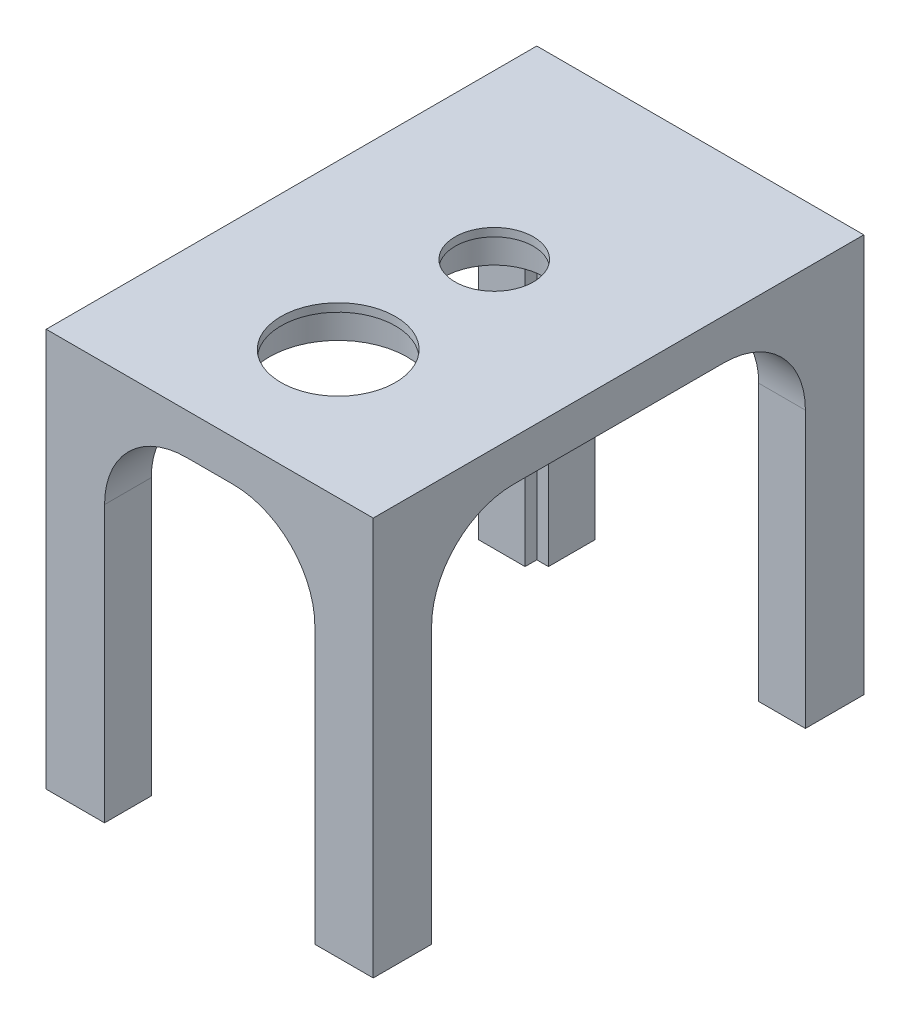
SolidWorks part; units mm, degrees
ref_plane "Front Plane" through (0, 0, 0) normal (0, 0, 1) x (1, 0, 0)
ref_plane "Top Plane" through (0, 0, 0) normal (0, 1, 0) x (1, 0, 0)
ref_plane "Right Plane" through (0, 0, 0) normal (1, 0, 0) x (0, 0, -1)
sketch "Sketch1" plane through (0, 0, 0) normal (0, 1, 0) x (1, 0, 0)
  line L1 (0, 0) -> (71.12, 0)
  line L2 (0, 0) -> (0, 106.68)
  line L3 (0, 106.68) -> (71.12, 106.68)
  line L4 (71.12, 0) -> (71.12, 106.68)
  dimension "D1" = 71.12
  dimension "D2" = 106.68
extrude "Boss-Extrude1" add sketch "Sketch1" along normal blind 87.884
shell "Shell1" thickness 10.16
sketch "Sketch3" plane through (0, 0, 0) normal (0, -1, 0) x (1, 0, 0)
  line L0 (0, 0) -> (71.12, 0) construction
  line L1 (0, -106.68) -> (0, 0) construction
  line L2 (6.35, -6.35) -> (6.35, -100.33) construction
  circle A0 centre (6.35, -6.35) radius 1.5875
  circle A1 centre (64.77, -6.35) radius 1.5875
  circle A2 centre (64.77, -100.33) radius 1.5875
  circle A3 centre (6.35, -100.33) radius 1.5875
  dimension "D1" = 6.35
  dimension "D2" = 6.35
  dimension "D5" = 93.98
  dimension "D3" = 2
  dimension "D4" = 2
extrude "Cut-Extrude1" cut sketch "Sketch3" against normal blind 10.16
sketch "Sketch4" plane through (0, 0, 0) normal (-1, 0, 0) x (0, 0, 1)
  line L0 (-106.68, 87.884) -> (0, 87.884) construction
  line L1 (-93.98, 0) -> (-12.7, 0)
  line L2 (-93.98, 0) -> (-93.98, 77.724)
  line L3 (-93.98, 77.724) -> (-12.7, 77.724)
  line L4 (-12.7, 0) -> (-12.7, 77.724)
  line L6 (0, 87.884) -> (0, 0) construction
  line L7 (-106.68, 87.884) -> (-106.68, 0) construction
  line L8 (-106.68, 0) -> (0, 0) construction
  dimension "D1" = 10.16
  dimension "D2" = 12.7
  dimension "D3" = 12.7
extrude "Cut-Extrude2" cut sketch "Sketch4" against normal through all
sketch "Sketch6" plane through (0, 0, 0) normal (0, -1, 0) x (1, 0, 0)
  line L0 (69.536, -6.35) -> (67.153, -2.2225)
  line L1 (11.116, -6.35) -> (8.733, -2.2225)
  line L2 (8.733, -2.2225) -> (3.967, -2.2225)
  line L3 (3.967, -2.2225) -> (1.584, -6.35)
  line L4 (1.584, -6.35) -> (3.967, -10.4775)
  line L5 (3.967, -10.4775) -> (8.733, -10.4775)
  line L6 (8.733, -10.4775) -> (11.116, -6.35)
  line L7 (67.153, -2.2225) -> (62.387, -2.2225)
  line L8 (62.387, -2.2225) -> (60.004, -6.35)
  line L9 (60.004, -6.35) -> (62.387, -10.4775)
  line L10 (62.387, -10.4775) -> (67.153, -10.4775)
  line L11 (67.153, -10.4775) -> (69.536, -6.35)
  line L12 (69.536, -100.33) -> (67.153, -96.2025)
  line L13 (67.153, -96.2025) -> (62.387, -96.2025)
  line L14 (62.387, -96.2025) -> (60.004, -100.33)
  line L15 (60.004, -100.33) -> (62.387, -104.4575)
  line L16 (62.387, -104.4575) -> (67.153, -104.4575)
  line L17 (67.153, -104.4575) -> (69.536, -100.33)
  line L18 (11.116, -100.33) -> (8.733, -96.2025)
  line L19 (8.733, -96.2025) -> (3.967, -96.2025)
  line L20 (3.967, -96.2025) -> (1.584, -100.33)
  line L21 (1.584, -100.33) -> (3.967, -104.4575)
  line L22 (3.967, -104.4575) -> (8.733, -104.4575)
  line L23 (8.733, -104.4575) -> (11.116, -100.33)
  circle A0 centre (6.35, -6.35) radius 4.1275 construction
  circle A1 centre (64.77, -6.35) radius 4.1275 construction
  circle A2 centre (64.77, -100.33) radius 4.1275 construction
  circle A3 centre (6.35, -100.33) radius 4.1275 construction
  dimension "D1" = 8.255
  dimension "D2" = 2
  dimension "D3" = 2
extrude "Cut-Extrude3" cut sketch "Sketch6" against normal blind 3.175
sketch "Sketch7" plane through (0, 0, -106.68) normal (0, 0, -1) x (-1, 0, 0)
  line L0 (-71.12, 87.884) -> (0, 87.884) construction
  line L1 (-58.42, 0) -> (-12.7, 0)
  line L2 (-58.42, 0) -> (-58.42, 77.724)
  line L3 (-58.42, 77.724) -> (-12.7, 77.724)
  line L4 (-12.7, 0) -> (-12.7, 77.724)
  line L6 (-71.12, 87.884) -> (-71.12, 0) construction
  line L7 (0, 87.884) -> (0, 0) construction
  dimension "D1" = 10.16
  dimension "D2" = 12.7
  dimension "D3" = 12.7
extrude "Cut-Extrude4" cut sketch "Sketch7" against normal through all and the other way through all
sketch "Sketch9" plane through (0, 87.884, 0) normal (0, 1, 0) x (1, 0, 0)
  line L1 (0, 0) -> (71.12, 0)
  line L2 (0, 0) -> (0, 106.68)
  line L3 (0, 106.68) -> (71.12, 106.68)
  line L4 (71.12, 0) -> (71.12, 106.68)
extrude "Cut-Extrude6" cut sketch "Sketch9" against normal blind 1.27
sketch "Sketch10" plane through (0, 77.724, 0) normal (0, -1, 0) x (-1, 0, 0)
  line L1 (-12.7, 0) -> (-58.42, 0) construction
  circle A0 centre (-35.56, 27.94) radius 14.986
  circle A1 centre (-35.56, 61.8744) radius 11.049
  point P4 (-35.56, 0)
  dimension "D1" = 29.972
  dimension "D3" = 22.098
  dimension "D2" = 27.94
  dimension "D4" = 33.9344
extrude "Cut-Extrude7" cut sketch "Sketch10" against normal blind 7.112
sketch "Sketch11" plane through (0, 77.724, 0) normal (0, -1, 0) x (1, 0, 0)
  circle A0 centre (35.56, -27.94) radius 12.446
  circle A1 centre (35.56, -61.8744) radius 8.509
  circle A2 centre (35.56, -27.94) radius 14.986 construction
  circle A3 centre (35.56, -61.8744) radius 11.049 construction
  dimension "D1" = 2.54
  dimension "D2" = 2.54
extrude "Cut-Extrude9" cut sketch "Sketch11" against normal through all
fillet "Fillet1" radius 17.78 8 edges at (66.04, 77.724, -93.98) (58.42, 77.724, -101.6) (5.08, 77.724, -93.98) (12.7, 77.724, -101.6) (66.04, 77.724, -12.7) (12.7, 77.724, -5.08) (58.42, 77.724, -5.08) (5.08, 77.724, -12.7)
